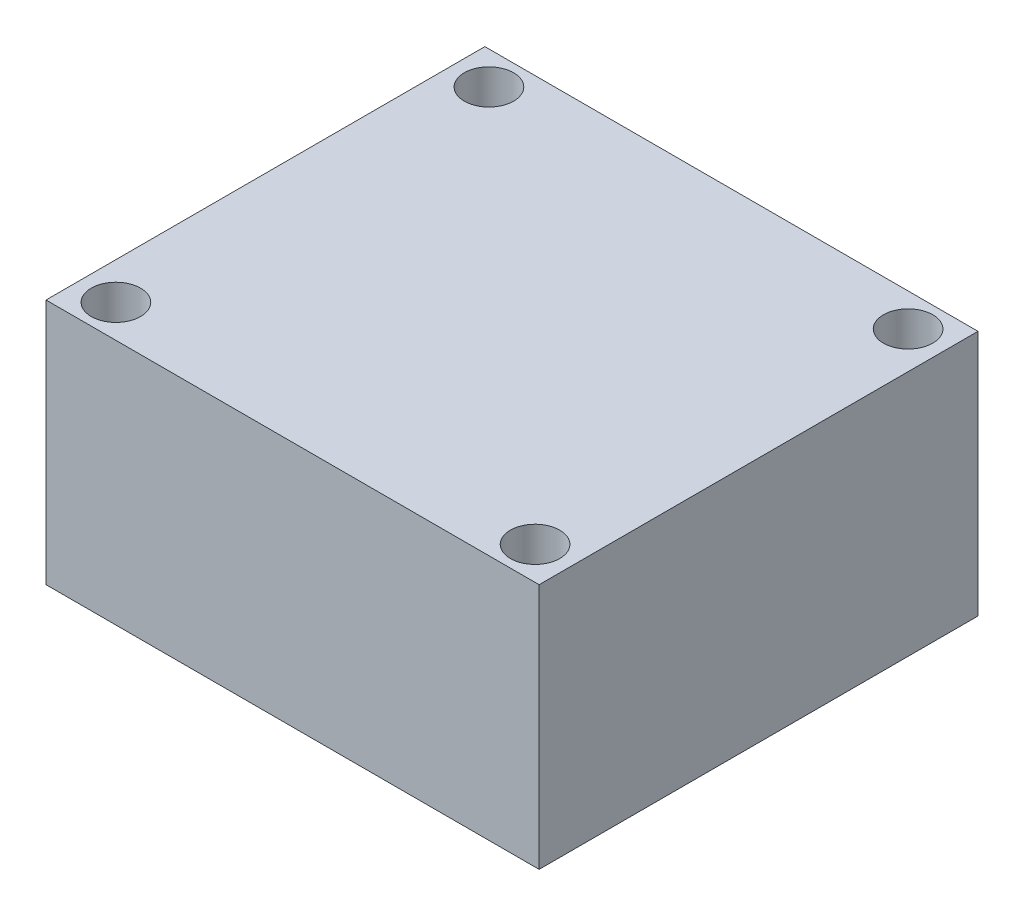
SolidWorks part; units mm, degrees
ref_plane "Front Plane" through (0, 0, 0) normal (0, 0, 1) x (1, 0, 0)
ref_plane "Top Plane" through (0, 0, 0) normal (0, 1, 0) x (1, 0, 0)
ref_plane "Right Plane" through (0, 0, 0) normal (1, 0, 0) x (0, 0, -1)
sketch "Sketch1" plane through (0, 0, 0) normal (0, 1, 0) x (1, 0, 0)
  line L0 (10, 16.465) -> (10, 1.0044) construction
  line L1 (0, 0) -> (20, 0)
  line L2 (0, 0) -> (0, 17.8)
  line L3 (0, 17.8) -> (20, 17.8)
  line L4 (20, 0) -> (20, 17.8)
  line L5 (0, 0) -> (20, 17.8) construction
  line L6 (0, 17.8) -> (20, 0) construction
  circle A0 centre (1.5, 16.465) radius 1
  circle A1 centre (1.5, 1.335) radius 1
  circle A2 centre (18.5, 1.335) radius 1
  circle A3 centre (18.5, 16.465) radius 1
  point P4 (10, 8.9)
  dimension "D3" = 2
  dimension "D1" = 17.8
  dimension "D2" = 20
  dimension "D4" = 1.5
extrude "Boss-Extrude1" add sketch "Sketch1" along normal blind 10
